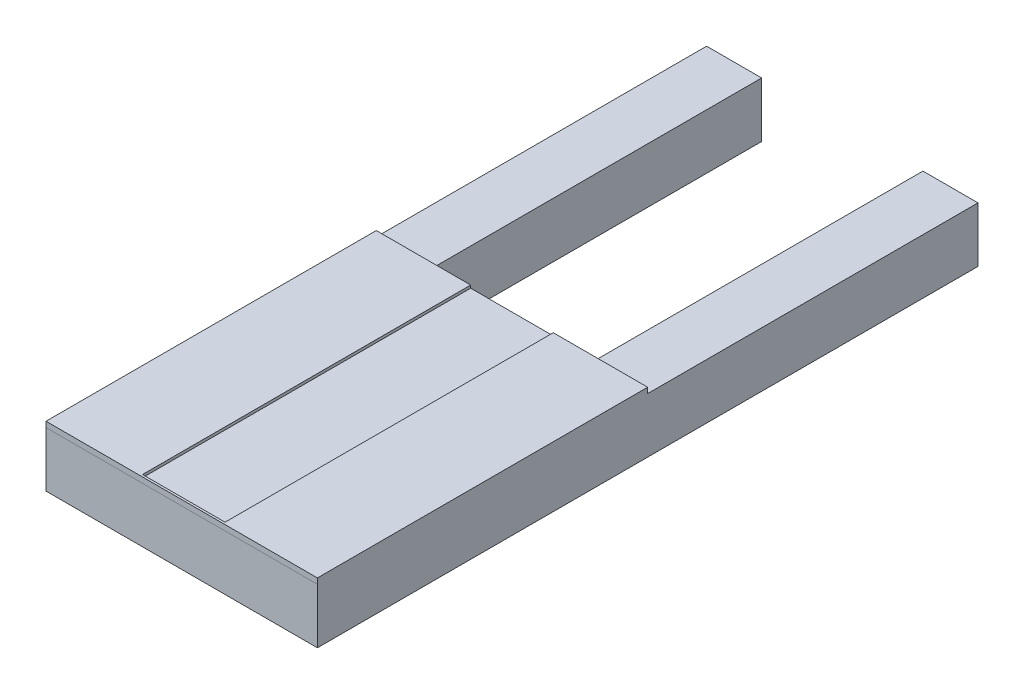
SolidWorks part; units mm, degrees
ref_plane "Front Plane" through (0, 0, 0) normal (0, 0, 1) x (1, 0, 0)
ref_plane "Top Plane" through (0, 0, 0) normal (0, 1, 0) x (1, 0, 0)
ref_plane "Right Plane" through (0, 0, 0) normal (1, 0, 0) x (0, 0, -1)
sketch "Sketch1" plane through (0, 0, 0) normal (0, 1, 0) x (1, 0, 0)
  line L0 (-64.6545, 257.8966) -> (-39.2545, 257.8966)
  line L1 (-39.2545, 257.8966) -> (-39.2545, -21.5034)
  line L2 (-39.2545, -21.5034) -> (35.1675, -21.5034)
  line L3 (35.1675, -21.5034) -> (35.1675, 257.8966)
  line L4 (35.1675, 257.8966) -> (60.5675, 257.8966)
  line L5 (60.5675, 257.8966) -> (60.5675, -46.9034)
  line L6 (60.5675, -46.9034) -> (-64.6545, -46.9034)
  line L7 (-64.6545, -46.9034) -> (-64.6545, 257.8966)
  dimension "D1" = 25.4
  dimension "D2" = 25.4
  dimension "D3" = 74.422
  dimension "D4" = 304.8
  dimension "D5" = 279.4
  dimension "D6" = 279.4
extrude "Boss-Extrude1" add sketch "Sketch1" along normal blind 25.4
sketch "Sketch3" plane through (0, 25.4, 0) normal (0, 1, 0) x (1, 0, 0)
  line L1 (-64.6545, 105.4871) -> (60.5675, 105.4871)
  line L2 (-64.6545, 105.4871) -> (-64.6545, -46.9129)
  line L3 (-64.6545, -46.9129) -> (60.5675, -46.9129)
  line L4 (60.5675, 105.4871) -> (60.5675, -46.9129)
  line L5 (-64.6545, 105.4871) -> (60.5675, -46.9129) construction
  line L6 (-64.6545, -46.9129) -> (60.5675, 105.4871) construction
  line L7 (-64.6545, 257.8966) -> (-64.6545, -46.9034) construction
  point P0 (-44.6998, 14.2043)
  dimension "D1" = 125.222
  dimension "D2" = 152.4
extrude "Boss-Extrude2" add sketch "Sketch3" along normal blind 2.54
sketch "Sketch5" plane through (0, 27.94, 0) normal (0, 1, 0) x (1, 0, 0)
  line L1 (-21.0935, 106.4591) -> (17.0065, 106.4591)
  line L2 (-21.0935, 106.4591) -> (-21.0935, -45.9409)
  line L3 (-21.0935, -45.9409) -> (17.0065, -45.9409)
  line L4 (17.0065, 106.4591) -> (17.0065, -45.9409)
  line L5 (-21.0935, 106.4591) -> (17.0065, -45.9409) construction
  line L6 (-21.0935, -45.9409) -> (17.0065, 106.4591) construction
  line L7 (60.5675, -46.9129) -> (60.5675, 105.4871) construction
  point P0 (-2.0435, 30.2591)
  dimension "D1" = 38.1
  dimension "D2" = 152.4
  dimension "D3" = 43.561
extrude "Cut-Extrude1" cut sketch "Sketch5" against normal blind 1.27
